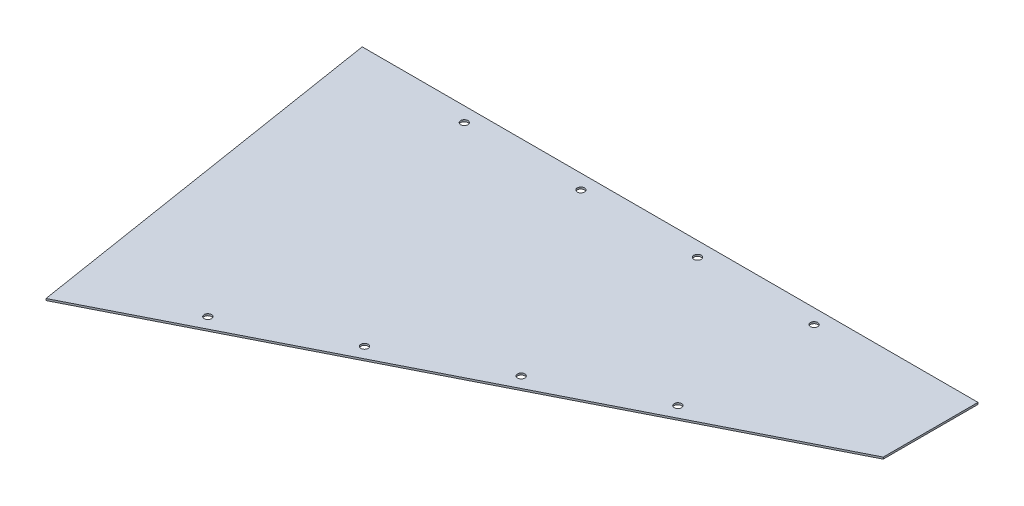
SolidWorks part; units mm, degrees
ref_plane "Front Plane" through (0, 0, 0) normal (0, 0, 1) x (1, 0, 0)
ref_plane "Top Plane" through (0, 0, 0) normal (0, 1, 0) x (1, 0, 0)
ref_plane "Right Plane" through (0, 0, 0) normal (1, 0, 0) x (0, 0, -1)
sketch "Sketch1" plane through (0, 0, 0) normal (0, 1, 0) x (1, 0, 0)
  line L0 (0, 0) -> (0, 165.1)
  line L1 (0, 165.1) -> (-1073.15, 165.1)
  line L2 (-1073.15, 165.1) -> (-968.887, -490.2328)
  line L3 (-968.887, -490.2328) -> (0, 0)
  dimension "D1" = 165.1
  dimension "D2" = 1073.15
  dimension "D3" = 663.575
  dimension "D4" = 1085.85
extrude "Boss-Extrude1" add sketch "Sketch1" along normal blind 3.175
sketch "Sketch2" plane through (0, 3.175, 0) normal (0, 1, 0) x (1, 0, 0)
  line L0 (956.479, 711.2) -> (-135.5629, 711.2) construction
  line L1 (956.479, 508) -> (956.479, 762) construction
  line L2 (-145.246, 762) -> (0, 0) construction
  line L3 (956.479, 762) -> (-145.246, 762) construction
  line L4 (956.479, 567.0249) -> (-1.926, 0) construction
  line L5 (0, 0) -> (97.84, 0) construction
  line L6 (97.84, 0) -> (956.479, 508) construction
  line L7 (956.479, 508) -> (930.6121, 551.7212) construction
  circle A0 centre (873.929, 711.2) radius 6.35
  circle A1 centre (492.929, 711.2) radius 6.35
  circle A2 centre (111.929, 711.2) radius 6.35
  circle A3 centre (859.5652, 509.6874) radius 6.35
  circle A4 centre (531.6563, 315.6854) radius 6.35
  circle A5 centre (203.7474, 121.6834) radius 6.35
  dimension "D2" = 12.7
  dimension "D7" = 381
  dimension "D8" = 381
  dimension "D1" = 50.8
  dimension "D3" = 82.55
  dimension "D4" = 381
  dimension "D5" = 381
  dimension "D6" = 50.8
  dimension "D9" = 82.55
sketch "Sketch3" plane through (0, 3.175, 0) normal (0, 1, 0) x (1, 0, 0)
  line L0 (0, 165.1) -> (-1073.15, 165.1) construction
  line L1 (-1073.15, 165.1) -> (-968.887, -490.2328) construction
  line L2 (-968.887, -490.2328) -> (0, 0) construction
  circle A0 centre (-869.7831, 139.7) radius 6.35
  circle A1 centre (-666.5831, 139.7) radius 6.35
  circle A2 centre (-463.3831, 139.7) radius 6.35
  circle A3 centre (-260.1831, 139.7) radius 6.35
  circle A4 centre (-800.5047, -376.5692) radius 6.35
  circle A5 centre (-619.1925, -284.8298) radius 6.35
  circle A6 centre (-437.8803, -193.0903) radius 6.35
  circle A7 centre (-256.5681, -101.3508) radius 6.35
  dimension "D1" = 25.4
  dimension "D2" = 196.85
  dimension "D4" = 184.15
  dimension "D5" = 25.4
  dimension "D3" = 4
  dimension "D6" = 4
extrude "Cut-Extrude1" cut sketch "Sketch3" against normal through all
